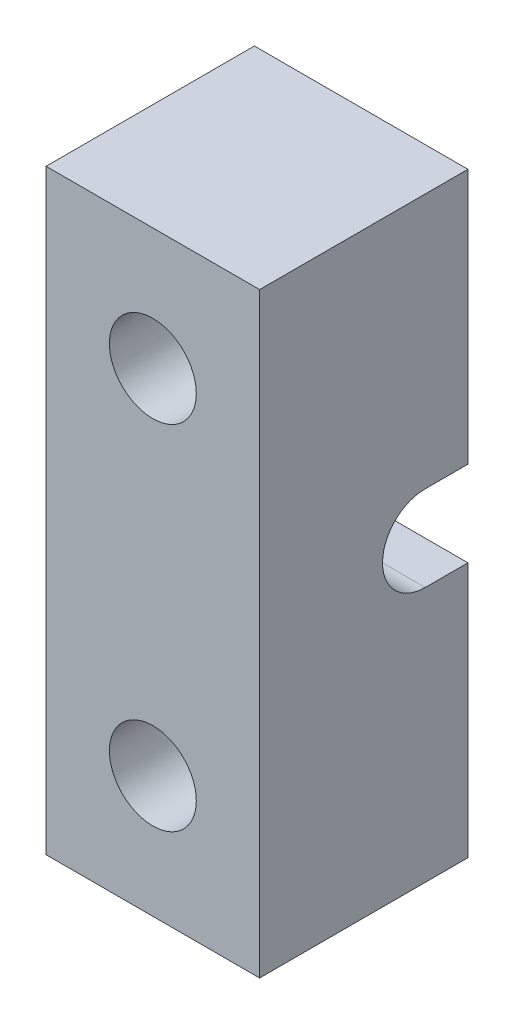
SolidWorks part; units mm, degrees
ref_plane "Front Plane" through (0, 0, 0) normal (0, 0, 1) x (1, 0, 0)
ref_plane "Top Plane" through (0, 0, 0) normal (0, 1, 0) x (1, 0, 0)
ref_plane "Right Plane" through (0, 0, 0) normal (1, 0, 0) x (0, 0, -1)
sketch "Sketch1" plane through (0, 0, 0) normal (0, 0, 1) x (1, 0, 0)
  line L0 (215.9, -15.5067) -> (215.9, -21.4656) construction
  line L1 (223.5888, -21.4656) -> (208.2112, -21.4656)
  line L2 (223.5888, -21.4656) -> (223.5888, 21.4656)
  line L3 (223.5888, 21.4656) -> (208.2112, 21.4656)
  line L4 (208.2112, -21.4656) -> (208.2112, 21.4656)
  line L5 (215.9, 15.5067) -> (215.9, 21.4656) construction
  line L6 (218.7067, -12.7) -> (223.5888, -12.7) construction
  line L7 (213.0933, -12.7) -> (208.2112, -12.7) construction
  circle A0 centre (215.9, -12.7) radius 2.8067 construction
  circle A1 centre (215.9, 12.7) radius 2.8067 construction
  circle A2 centre (215.9, -12.7) radius 3.1292
  circle A3 centre (215.9, 12.7) radius 3.1292
extrude "Boss-Extrude1" add sketch "Sketch1" along normal blind 15
sketch "Sketch2" plane through (223.5888, 0, 0) normal (1, 0, 0) x (0, 0, -1)
  line L0 (0, 0) -> (-15, 0) construction
  line L1 (-15, -21.4656) -> (-15, 21.4656) construction
  line L2 (0, 0) -> (-3.075, 0) construction
  line L3 (0, -3.075) -> (-3.075, -3.075)
  line L4 (0, 3.075) -> (-3.075, 3.075)
  line L5 (0, -21.4656) -> (0, 21.4656) construction
  arc A0 (0, -3.075) -> (0, 3.075) centre (0, 0) ccw
  arc A1 (-3.075, 3.075) -> (-3.075, -3.075) centre (-3.075, 0) ccw
  point P7 (-1.5375, 0)
  point P12 (0, 0)
  dimension "D1" = 3.075
  dimension "D2" = 3.075
extrude "Cut-Extrude1" cut sketch "Sketch2" against normal through all both
